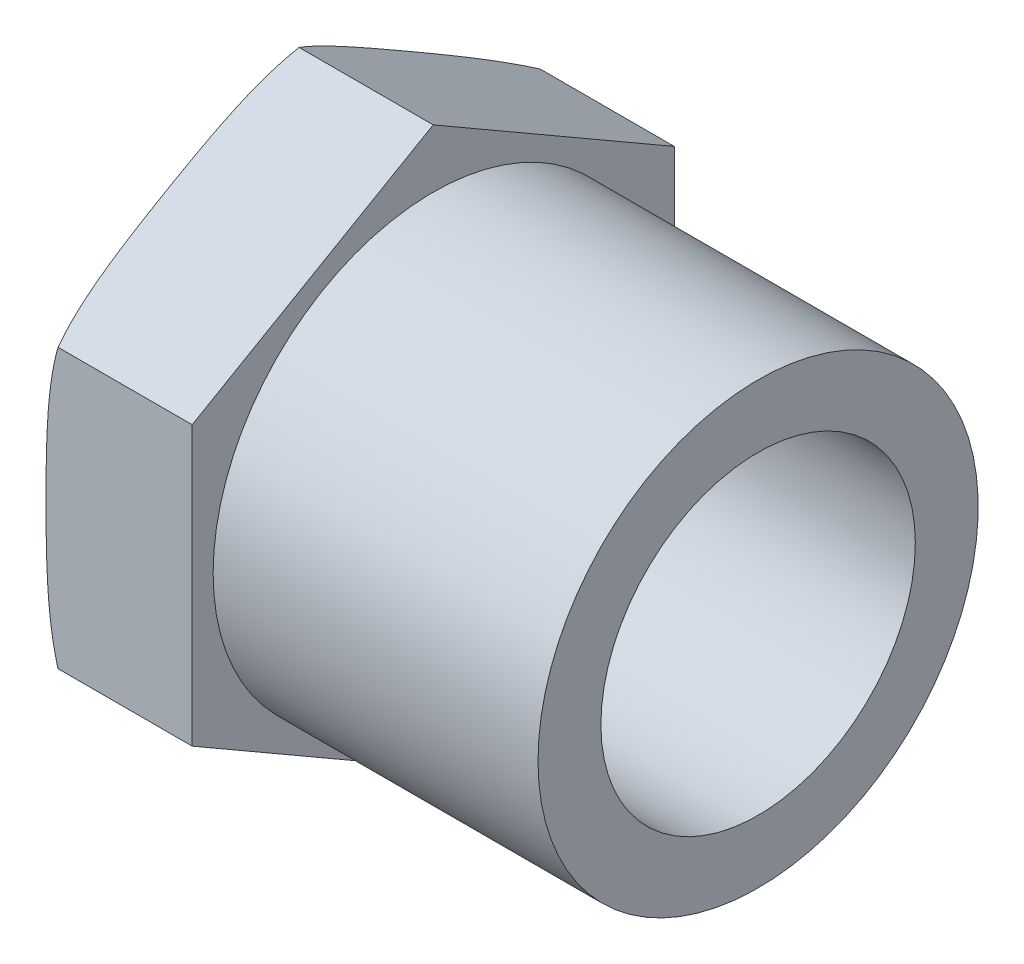
SolidWorks part; units mm, degrees
ref_plane "Front Plane" through (0, 0, 0) normal (0, 0, 1) x (1, 0, 0)
ref_plane "Top Plane" through (0, 0, 0) normal (0, 1, 0) x (1, 0, 0)
ref_plane "Right Plane" through (0, 0, 0) normal (1, 0, 0) x (0, 0, -1)
sketch "Sketch1" plane through (0, 0, 0) normal (0, 0, 1) x (1, 0, 0)
  line L0 (0, 0) -> (23.1571, 0) construction
  line L1 (0, 6.5) -> (0, 10.5)
  line L2 (0, 10.5) -> (22.5, 10.5)
  line L3 (22.5, 10.5) -> (22.5, 7.5)
  line L4 (22.5, 7.5) -> (10.5, 7.5)
  line L5 (10, 7) -> (10, 6.5)
  line L6 (10, 6.5) -> (0, 6.5)
  arc A0 (10.5, 7.5) -> (10, 7) centre (10.5, 7) ccw
  point P11 (10, 7.5)
  dimension "D6" = 0.5
  dimension "D1" = 6.5
  dimension "D2" = 10.5
  dimension "D3" = 3
  dimension "D4" = 12.5
  dimension "D5" = 22.5
revolve "Revolve1" add sketch "Sketch1" angle 360 about L0
sketch "Sketch2" plane through (0, 0, 0) normal (-1, 0, 0) x (0, 0, 1)
  line L1 (0, 13.2791) -> (-11.5, 6.6395)
  line L2 (-11.5, 6.6395) -> (-11.5, -6.6395)
  line L3 (-11.5, -6.6395) -> (0, -13.2791)
  line L4 (0, -13.2791) -> (11.5, -6.6395)
  line L5 (11.5, -6.6395) -> (11.5, 6.6395)
  line L6 (11.5, 6.6395) -> (0, 13.2791)
  circle A0 centre (0, 0) radius 11.5 construction
  circle A1 centre (0, 0) radius 10.5 construction
  circle A2 centre (0, 0) radius 6.5 construction
  circle A3 centre (0, 0) radius 6.5
  dimension "D1" = 1
  dimension "D2" = 23
extrude "Boss-Extrude1" add sketch "Sketch2" against normal blind 7
sketch "Sketch5" plane through (0, 0, 0) normal (0, 0, 1) x (1, 0, 0)
  line L0 (0, 6.6395) -> (0, 13.2791) construction
  line L2 (7, 13.2791) -> (0, 13.2791) construction
  line L3 (0.6, 13.2791) -> (0, 13.2791)
  line L4 (0, 13.2791) -> (0, 11)
  arc A0 (0, 11) -> (0.6, 13.2791) centre (4.6284, 11) cw
  dimension "D1" = 11
  dimension "D2" = 0.6
sketch "Sketch6" plane through (0, 0, 0) normal (-1, 0, 0) x (0, 0, 1)
  circle A0 centre (0, 0) radius 11.5 construction
  circle A1 centre (0, 0) radius 11.5
sweep "Cut-Sweep1" cut profiles "Sketch5" path "Sketch6"
